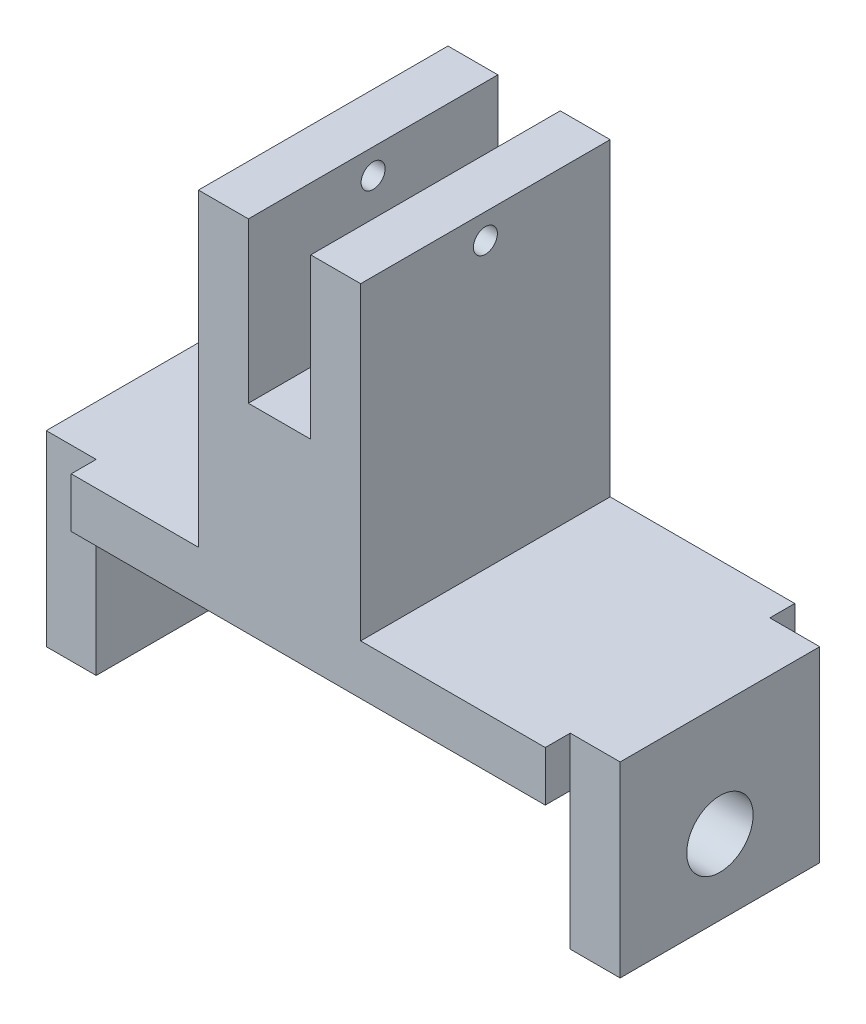
SolidWorks part; units mm, degrees
ref_plane "Front Plane" through (0, 0, 0) normal (0, 0, 1) x (1, 0, 0)
ref_plane "Top Plane" through (0, 0, 0) normal (0, 1, 0) x (1, 0, 0)
ref_plane "Right Plane" through (0, 0, 0) normal (1, 0, 0) x (0, 0, -1)
sketch "Sketch1" plane through (0, 0, 0) normal (0, 1, 0) x (1, 0, 0)
  line L1 (0, 0) -> (48.26, 0)
  line L2 (0, 0) -> (0, 25.4)
  line L3 (0, 25.4) -> (48.26, 25.4)
  line L4 (48.26, 0) -> (48.26, 25.4)
  dimension "D1" = 25.4
  dimension "D2" = 48.26
extrude "Boss-Extrude1" add sketch "Sketch1" along normal blind 5.08
sketch "Sketch3" plane through (0, 5.08, 0) normal (0, 1, 0) x (1, 0, 0)
  line L0 (48.26, 0) -> (48.26, 25.4) construction
  line L1 (29.464, 25.4) -> (24.384, 25.4)
  line L3 (29.464, 0) -> (24.384, 0)
  line L4 (24.384, 25.4) -> (24.384, 0)
  line L5 (29.464, 0) -> (29.464, 25.4)
  line L6 (18.034, 25.4) -> (12.954, 25.4)
  line L7 (18.034, 25.4) -> (18.034, 0)
  line L8 (18.034, 0) -> (12.954, 0)
  line L9 (12.954, 25.4) -> (12.954, 0)
  line L10 (48.26, 25.4) -> (0, 25.4) construction
  line L12 (0, 0) -> (48.26, 0) construction
  dimension "D1" = 5.08
  dimension "D3" = 5.08
  dimension "D4" = 6.35
  dimension "D7" = 30.226
extrude "Boss-Extrude2" add sketch "Sketch3" along normal blind 31.496
sketch "Sketch4" plane through (29.464, 0, 0) normal (1, 0, 0) x (0, 0, -1)
  line L0 (0, 36.576) -> (25.4, 36.576) construction
  line L2 (0, 36.576) -> (25.4, 36.576) construction
  circle A0 centre (12.7, 34.036) radius 1.2192
  point P6 (12.7, 36.576)
  dimension "D1" = 2.4384
  dimension "D2" = 2.54
extrude "Cut-Extrude2" cut sketch "Sketch4" against normal through all
sketch "Sketch5" plane through (29.464, 0, 0) normal (1, 0, 0) x (0, 0, -1)
  line L0 (0, 20.32) -> (25.4, 20.32)
  line L1 (0, 36.576) -> (0, 5.08) construction
  line L2 (25.4, 36.576) -> (25.4, 5.08) construction
  line L3 (0, 5.08) -> (25.4, 5.08) construction
  line L4 (0, 5.08) -> (0, 20.32)
  line L5 (25.4, 5.08) -> (25.4, 20.32)
  line L6 (0, 5.08) -> (25.4, 5.08)
  point P9 (0, 0)
  point P15 (0, 0)
  point P16 (0, 0)
  point P17 (0, 0)
  dimension "D1" = 15.24
extrude "Boss-Extrude3" add sketch "Sketch5" against normal up to surface (16.51 mm away) up to face at (12.954, 34.036, -13.9192)
sketch "Sketch6" plane through (0, 0, 0) normal (-1, 0, 0) x (0, 0, 1)
  line L0 (-22.86, 5.08) -> (-22.86, -13.97)
  line L1 (-22.86, 5.08) -> (-2.54, 5.08)
  line L3 (-22.86, -13.97) -> (-2.54, -13.97)
  line L5 (-2.54, 5.08) -> (-2.54, -13.97)
  line L6 (-25.4, 5.08) -> (-25.4, 0) construction
  line L7 (-25.4, 5.08) -> (0, 5.08) construction
  dimension "D1" = 2.54
  dimension "D2" = 19.05
  dimension "D3" = 20.32
extrude "Boss-Extrude4" add sketch "Sketch6" along normal blind 5.08
sketch "Sketch7" plane through (48.26, 0, 0) normal (1, 0, 0) x (0, 0, -1)
  line L0 (2.54, 5.08) -> (2.54, -13.97)
  line L1 (2.54, 5.08) -> (22.86, 5.08)
  line L3 (2.54, -13.97) -> (22.86, -13.97)
  line L5 (22.86, 5.08) -> (22.86, -13.97)
  line L6 (0, 5.08) -> (0, 0) construction
  line L8 (0, 5.08) -> (25.4, 5.08) construction
  dimension "D1" = 20.32
  dimension "D2" = 2.54
  dimension "D3" = 19.05
extrude "Boss-Extrude5" add sketch "Sketch7" along normal blind 5.08
sketch "Sketch8" plane through (53.34, 0, 0) normal (1, 0, 0) x (0, 0, -1)
  line L0 (2.54, 5.08) -> (2.54, -13.97) construction
  line L1 (2.54, -13.97) -> (22.86, -13.97) construction
  circle A0 centre (12.7, -6.35) radius 3.3782
  dimension "D1" = 6.7564
  dimension "D2" = 10.16
  dimension "D3" = 7.62
extrude "Cut-Extrude3" cut sketch "Sketch8" against normal blind 6.35
sketch "Sketch9" plane through (-5.08, 0, 0) normal (-1, 0, 0) x (0, 0, 1)
  line L0 (-22.86, 5.08) -> (-22.86, -13.97) construction
  line L1 (-22.86, -13.97) -> (-2.54, -13.97) construction
  circle A0 centre (-12.7, -6.35) radius 3.3782
  dimension "D1" = 6.7564
  dimension "D2" = 10.16
  dimension "D3" = 7.62
extrude "Cut-Extrude4" cut sketch "Sketch9" against normal blind 6.35
